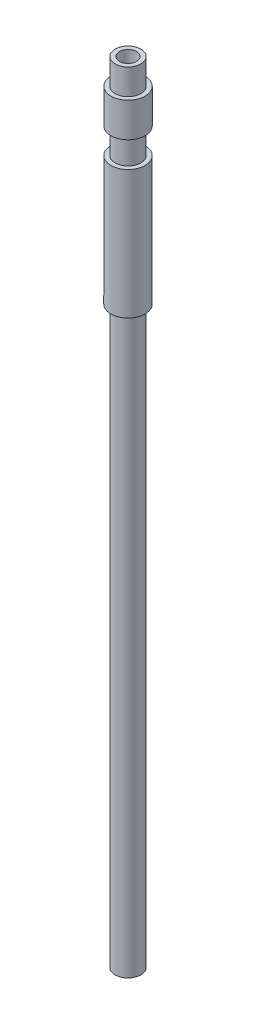
SolidWorks part; units mm, degrees
material "Простая углеродистая сталь"
ref_plane "Спереди" through (0, 0, 0) normal (0, 0, 1) x (1, 0, 0)
ref_plane "Сверху" through (0, 0, 0) normal (0, 1, 0) x (1, 0, 0)
ref_plane "Справа" through (0, 0, 0) normal (1, 0, 0) x (0, 0, -1)
sketch "Эскиз1" plane through (0, 0, 0) normal (0, 1, 0) x (1, 0, 0)
  circle A0 centre (0, 0) radius 1
  circle A1 centre (0, 0) radius 2
  dimension "D1" = 4
  dimension "D2" = 2
extrude "Бобышка-Вытянуть1" add sketch "Эскиз1" along normal blind 92
sketch "Эскиз2" plane through (0, 0, 0) normal (0, 0, 1) x (1, 0, 0)
  line L0 (2, 92) -> (1.5, 92)
  line L1 (2, 92) -> (2, 89)
  line L2 (1.5, 92) -> (1.5, 89)
  line L3 (2, 89) -> (1.5, 89)
  line L4 (2, 85) -> (1.5, 85)
  line L5 (2, 85) -> (2, 82)
  line L6 (1.5, 85) -> (1.5, 82)
  line L7 (2, 82) -> (1.5, 82)
  line L8 (1, 92) -> (-1, 92) construction
  line L9 (1, 92) -> (-1, 92) construction
  line L10 (0, 92) -> (0, 0) construction
  line L11 (-2, 0) -> (2, 0) construction
  line L12 (-2, 0) -> (2, 0) construction
  dimension "D1" = 3
  dimension "D2" = 0.5
  dimension "D3" = 2
  dimension "D4" = 7
revolve "Вырез-Повернуть1" cut sketch "Эскиз2" angle 360 about L10
sketch "Эскиз3" plane through (0, 0, 0) normal (0, 0, 1) x (1, 0, 0)
  line L0 (2, 0) -> (1.5, 0)
  line L1 (2, 0) -> (2, 67)
  line L2 (1.5, 0) -> (1.5, 67)
  line L3 (2, 67) -> (1.5, 67)
  line L4 (2, 82) -> (-2, 82) construction
  line L5 (0, 0) -> (0, 92) construction
  line L6 (1, 92) -> (-1, 92) construction
  line L7 (1, 92) -> (-1, 92) construction
  dimension "D1" = 15
  dimension "D2" = 0.5
revolve "Вырез-Повернуть2" cut sketch "Эскиз3" angle 360 about L5
sketch "Эскиз4" plane through (0, 0, 0) normal (0, 0, 1) x (1, 0, 0)
  line L0 (-2, 80) -> (2, 80) construction
  line L1 (1.5, 92) -> (-1.5, 92) construction
  line L2 (1.5, 92) -> (-1.5, 92) construction
  line L3 (2, 82) -> (-2, 82) construction
  line L4 (2, 82) -> (-2, 82) construction
  line L5 (-2, 82) -> (-2, 67) construction
  line L6 (2, 67) -> (2, 82) construction
  dimension "D1" = 12
ref_plane "Плоскость1" through (0, 80, 0) normal (0, 1, 0) x (1, 0, 0)
sketch "Эскиз5" plane through (0, 80, 0) normal (0, 1, 0) x (1, 0, 0)
  line L0 (-2, 0) -> (2, 0) construction
  circle A0 centre (0, 0) radius 2 construction
